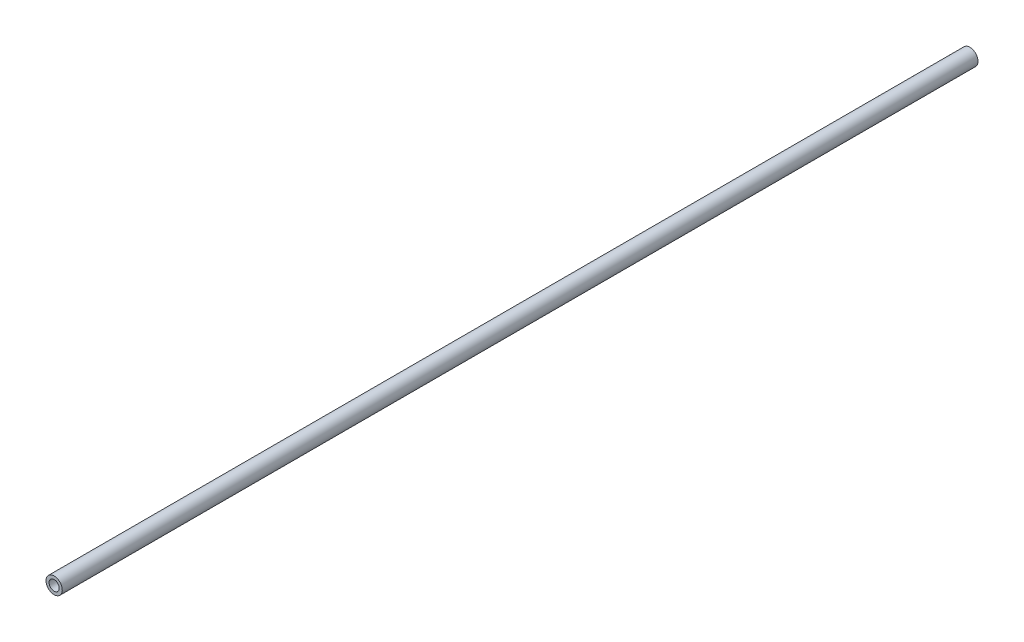
SolidWorks part; units mm, degrees
ref_plane "Front" through (0, 0, 0) normal (0, 0, 1) x (1, 0, 0)
ref_plane "Top" through (0, 0, 0) normal (0, 1, 0) x (1, 0, 0)
ref_plane "Right" through (0, 0, 0) normal (1, 0, 0) x (0, 0, -1)
sketch "Croquis1" plane through (0, 0, 0) normal (0, 0, 1) x (1, 0, 0)
  circle A0 centre (0, 0) radius 4
  dimension "D1" = 8
extrude "Saliente-Extruir1" add sketch "Croquis1" along normal blind 450
hole_wizard "Taladro roscado M6x1.01" positions "Croquis2" profile "Croquis3" tap size "M6x1.0" standard "Ansi Metric"
sketch "Croquis2" plane through (0, 0, 450) normal (0, 0, 1) x (1, 0, 0)
  point P0 (0, 0)
sketch "Croquis3" plane through (0, 0, 450) normal (1, 0, 0) x (0, -1, 0)
  line L0 (0, 0) -> (0, 18.5022)
  line L1 (0, 18.5022) -> (2.5, 17)
  line L2 (2.5, 17) -> (2.5, 0)
  line L5 (2.5, 0) -> (0, 0)
  line L10 (0, 18.5022) -> (-2.5, 17) construction
  line L11 (0, -6.35) -> (0, 107.95) construction
  dimension "Diámetro de perforador para roscar" = 5
  dimension "Profundidad de perforador para roscar" = 17
  dimension "Ángulo de perforador" = 118
cosmetic thread "Rosca de taladro3" parameters "D1"=12, "D2"=6
hole_wizard "Taladro roscado M6x1.02" positions "Croquis4" profile "Croquis5" tap size "M6x1.0" standard "Ansi Metric"
sketch "Croquis4" plane through (0, 0, 0) normal (0, 0, -1) x (-1, 0, 0)
  point P0 (0, 0)
sketch "Croquis5" plane through (0, 0, 0) normal (1, 0, 0) x (0, 1, 0)
  line L0 (0, 0) -> (0, 18.5022)
  line L1 (0, 18.5022) -> (2.5, 17)
  line L2 (2.5, 17) -> (2.5, 0)
  line L5 (2.5, 0) -> (0, 0)
  line L10 (0, 18.5022) -> (-2.5, 17) construction
  line L11 (0, -6.35) -> (0, 107.95) construction
  dimension "Diámetro de perforador para roscar" = 5
  dimension "Profundidad de perforador para roscar" = 17
  dimension "Ángulo de perforador" = 118
cosmetic thread "Rosca de taladro4" parameters "D1"=12, "D2"=6
